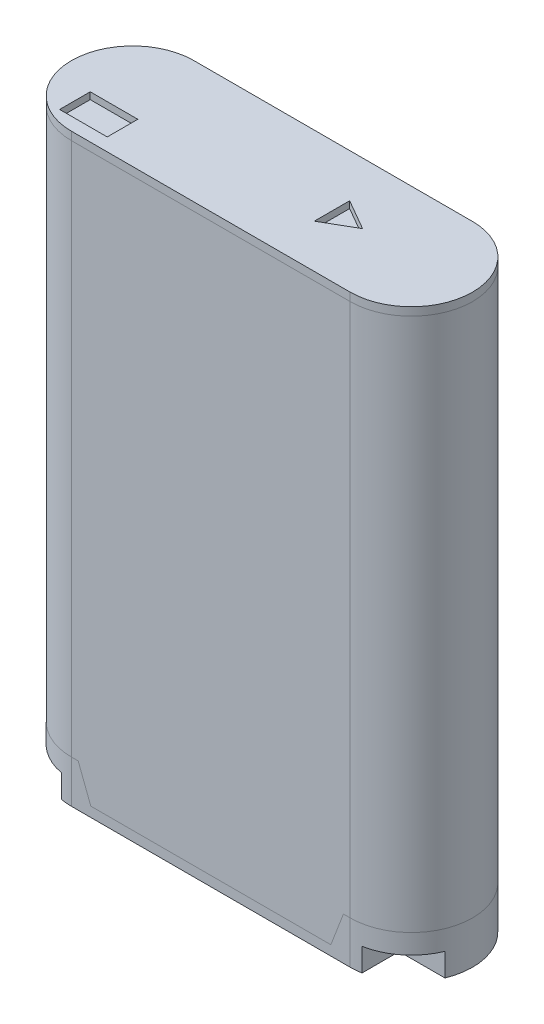
SolidWorks part; units mm, degrees
ref_plane "Front Plane" through (0, 0, 0) normal (0, 0, 1) x (1, 0, 0)
ref_plane "Top Plane" through (0, 0, 0) normal (0, 1, 0) x (1, 0, 0)
ref_plane "Right Plane" through (0, 0, 0) normal (1, 0, 0) x (0, 0, -1)
sketch "Sketch1" plane through (0, 0, 0) normal (0, 1, 0) x (1, 0, 0)
  line L0 (-10.25, 0) -> (10.25, 0) construction
  line L1 (-10.25, 4.5) -> (10.25, 4.5)
  line L2 (-10.25, -4.5) -> (10.25, -4.5)
  arc A0 (-10.25, 4.5) -> (-10.25, -4.5) centre (-10.25, 0) ccw
  arc A1 (10.25, -4.5) -> (10.25, 4.5) centre (10.25, 0) ccw
  point P3 (0, 0)
  point P8 (14.75, 0)
  point P9 (-14.75, 0)
  dimension "D1" = 9
  dimension "D2" = 29.5
extrude "Boss-Extrude1" add sketch "Sketch1" along normal blind 43
sketch "Sketch2" plane through (0, 43, 0) normal (0, 1, 0) x (1, 0, 0)
  line L0 (4.4102, 0) -> (6.6619, 0) construction
  line L1 (-12.0693, -1.2996) -> (-8.5693, -1.2996)
  line L2 (-12.0693, -1.2996) -> (-12.0693, -3.5496)
  line L3 (-12.0693, -3.5496) -> (-8.5693, -3.5496)
  line L4 (-8.5693, -1.2996) -> (-8.5693, -3.5496)
  line L5 (6.6619, 0) -> (4.4102, 1.3)
  line L6 (4.4102, 1.3) -> (4.4102, -1.3)
  line L7 (6.6619, 0) -> (4.4102, -1.3)
  dimension "D1" = 2.6
  dimension "D2" = 2.6
  dimension "D3" = 3.5
  dimension "D4" = 2.25
extrude "Cut-Extrude1" cut sketch "Sketch2" against normal blind 0.5
sketch "Sketch3" plane through (0, 0, 0) normal (0, -1, 0) x (1, 0, 0)
  line L0 (10.25, -4.5) -> (-10.25, -4.5) construction
  line L1 (-11.15, 0) -> (-7, 0)
  line L2 (-11.15, 0) -> (-11.15, -3.2)
  line L3 (-11.15, -3.2) -> (-7, -3.2)
  line L4 (-7, 0) -> (-7, -3.2)
  line L5 (-5.7, 0) -> (-2.7, 0)
  line L6 (-5.7, 0) -> (-5.7, -3.2)
  line L7 (-5.7, -3.2) -> (-2.7, -3.2)
  line L8 (-2.7, 0) -> (-2.7, -3.2)
  line L9 (-1.3, 0) -> (2.85, 0)
  line L10 (-1.3, 0) -> (-1.3, -3.2)
  line L11 (-1.3, -3.2) -> (2.85, -3.2)
  line L12 (2.85, 0) -> (2.85, -3.2)
  line L13 (3.85, 0) -> (6.85, 0)
  line L14 (3.85, 0) -> (3.85, -3.2)
  line L15 (3.85, -3.2) -> (6.85, -3.2)
  line L16 (6.85, 0) -> (6.85, -3.2)
  arc A0 (-10.25, 4.5) -> (-10.25, -4.5) centre (-10.25, 0) ccw construction
  point P16 (-14.75, 0)
  dimension "D1" = 18
  dimension "D2" = 3
  dimension "D3" = 3.2
  dimension "D4" = 4.15
  dimension "D5" = 1
  dimension "D6" = 1.3
  dimension "D7" = 3.6
  dimension "D8" = 1.3
extrude "Cut-Extrude2" cut sketch "Sketch3" against normal blind 0.75
sketch "Sketch5" plane through (0, 0, 0) normal (0, -1, 0) x (1, 0, 0)
  line L0 (5.35, 0) -> (5.35, 2.25) construction
  line L1 (6.85, 0) -> (3.85, 0) construction
  line L2 (0.775, 0) -> (0.775, 2.25) construction
  line L3 (2.85, 0) -> (-1.3, 0) construction
  line L4 (-4.2, 0) -> (-4.2, 2.25) construction
  line L5 (-2.7, 0) -> (-5.7, 0) construction
  line L6 (-9.075, 0) -> (-9.075, 2.25) construction
  line L7 (-7, 0) -> (-11.15, 0) construction
  line L8 (-9.075, 2.25) -> (-9.075, 4.5) construction
  line L9 (-10.25, 4.5) -> (10.25, 4.5) construction
  circle A0 centre (-9.075, 2.25) radius 1.25
  circle A1 centre (-4.2, 2.25) radius 1.25
  circle A2 centre (0.775, 2.25) radius 1.25
  circle A3 centre (5.35, 2.25) radius 1.25
  dimension "D1" = 2.5
extrude "Cut-Extrude3" cut sketch "Sketch5" against normal blind 0.25
sketch "Sketch6" plane through (0, 0.25, 0) normal (0, -1, 0) x (1, 0, 0)
  line L0 (6.2348, 3.0483) -> (2.915, 3.0483) construction
  line L1 (-3.8112, 3.0483) -> (-6.1079, 3.0483) construction
  line L2 (-9.3191, 2.0805) -> (-9.9246, 2.0805)
  line L3 (1.4711, 2.0276) -> (0.1441, 2.0276)
  line L4 (1.4711, 2.0276) -> (1.4711, 2.5124)
  line L5 (1.4711, 2.5124) -> (0.1441, 2.5124)
  line L6 (0.1441, 2.0276) -> (0.1441, 2.5124)
  line L7 (-8.1946, 2.0805) -> (-8.8146, 2.0805)
  line L8 (-8.1946, 2.0805) -> (-8.1946, 2.5124)
  line L9 (-8.1946, 2.5124) -> (-8.8146, 2.5124)
  line L10 (-9.9246, 2.0805) -> (-9.9246, 2.5124)
  line L11 (-9.3191, 1.3236) -> (-8.8146, 1.3236)
  line L12 (-9.3191, 1.3236) -> (-9.3191, 2.0805)
  line L13 (-9.3191, 3.2194) -> (-8.8146, 3.2194)
  line L14 (-8.8146, 1.3236) -> (-8.8146, 2.0805)
  line L15 (-9.3191, 2.5124) -> (-9.3191, 3.2194)
  line L16 (-8.8146, 2.5124) -> (-8.8146, 3.2194)
  line L17 (-9.3191, 2.5124) -> (-9.9246, 2.5124)
  text T0 "<b>C</b>" font "Century Gothic" height 1.5
  text T1 "<b>T</b>" font "Century Gothic" height 1.5
extrude "Boss-Extrude2" add sketch "Sketch6" along normal blind 0.25
sketch "Sketch7" plane through (0, 0, 0) normal (0, -1, 0) x (1, 0, 0)
  line L0 (-10.25, 4.5) -> (10.25, 4.5) construction
  line L1 (-14.75, 4.5) -> (-11.05, 4.5)
  line L2 (-14.75, 4.5) -> (-14.75, 1.7)
  line L3 (-14.75, 1.7) -> (-11.05, 1.7)
  line L4 (-11.05, 4.5) -> (-11.05, 1.7)
  line L5 (10.25, -4.5) -> (-10.25, -4.5) construction
  line L6 (0, 0) -> (0, 7.4102) construction
  line L7 (11.05, 4.5) -> (11.05, 1.7)
  line L8 (14.75, 1.7) -> (11.05, 1.7)
  line L9 (14.75, 4.5) -> (14.75, 1.7)
  line L10 (14.75, 4.5) -> (11.05, 4.5)
  arc A0 (-10.25, 4.5) -> (-10.25, -4.5) centre (-10.25, 0) ccw construction
  arc A1 (10.25, -4.5) -> (10.25, 4.5) centre (10.25, 0) ccw construction
  point P4 (-14.75, 0)
  point P11 (14.75, 0)
  dimension "D1" = 25.8
  dimension "D2" = 6.2
extrude "Cut-Extrude4" cut sketch "Sketch7" against normal blind 1.7
sketch "Sketch8" plane through (0, 0, -4.5) normal (0, 0, -1) x (-1, 0, 0)
  line L0 (0, 0) -> (0, 43) construction
  line L1 (-10.25, 43) -> (10.25, 43) construction
  line L2 (-14.75, 42.3974) -> (14.75, 42.3974)
  line L3 (-14.75, 43) -> (-14.75, 0) construction
  line L4 (14.75, 0) -> (14.75, 43) construction
  line L5 (-14.75, 3.1417) -> (-9.7535, 3.1417)
  line L6 (-9.7535, 3.1417) -> (-8.8265, 0.7235)
  line L7 (-8.8265, 0.7235) -> (8.8265, 0.7235)
  line L8 (9.7535, 3.1417) -> (8.8265, 0.7235)
  line L9 (14.75, 3.1417) -> (9.7535, 3.1417)
  point P16 (0, 0.7235)
split line "Split Line1"
